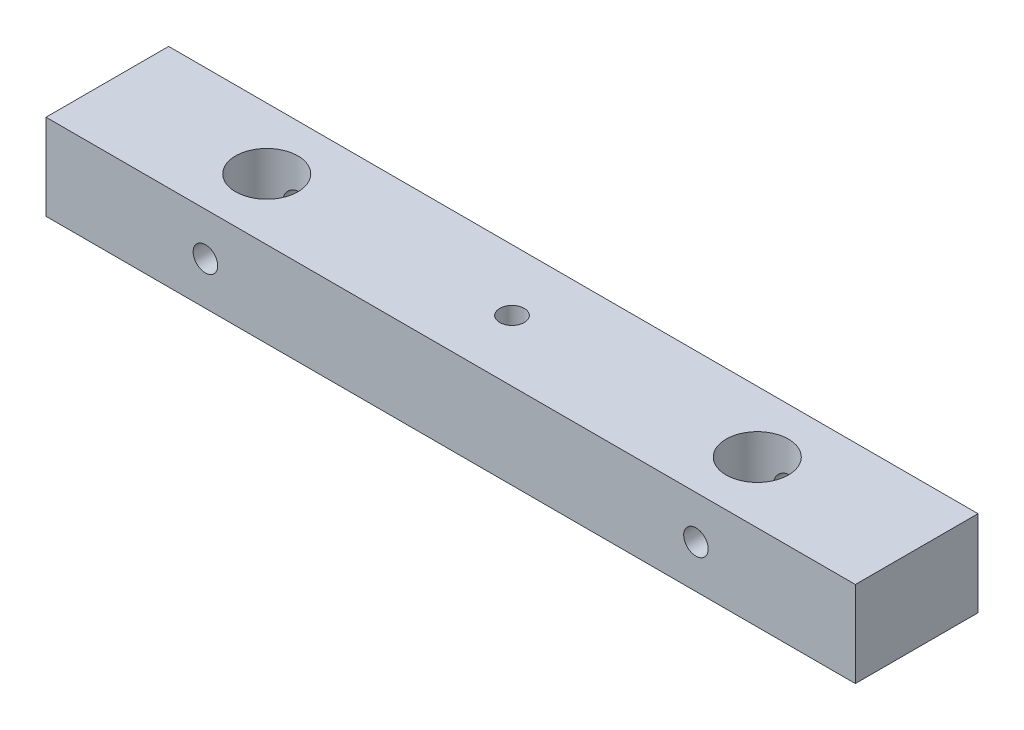
SolidWorks part; units mm, degrees
ref_plane "Front" through (0, 0, 0) normal (0, 0, 1) x (1, 0, 0)
ref_plane "Top" through (0, 0, 0) normal (0, 1, 0) x (1, 0, 0)
ref_plane "Right" through (0, 0, 0) normal (1, 0, 0) x (0, 0, -1)
sketch "Sketch1" plane through (0, 0, 0) normal (0, 1, 0) x (1, 0, 0)
  line L1 (165, 25) -> (-165, 25)
  line L2 (165, 25) -> (165, -25)
  line L3 (165, -25) -> (-165, -25)
  line L4 (-165, 25) -> (-165, -25)
  line L5 (165, 25) -> (-165, -25) construction
  line L6 (165, -25) -> (-165, 25) construction
  point P0 (0, 0)
  dimension "D1" = 330
  dimension "D2" = 50
extrude "Boss-Extrude1" add sketch "Sketch1" along normal blind 35
sketch "Sketch2" plane through (0, 35, 0) normal (0, 1, 0) x (1, 0, 0)
  line L0 (100, 0) -> (-100, 0) construction
  circle A0 centre (-100, 0) radius 12.7
  circle A1 centre (100, 0) radius 12.7
  point P4 (0, 0)
  dimension "D1" = 200
extrude "Cut-Extrude1" cut sketch "Sketch2" against normal blind 70
sketch "Sketch3" plane through (0, 0, 25) normal (0, 0, 1) x (1, 0, 0)
  line L0 (100, 17.5) -> (-100, 17.5) construction
  line L1 (100, 0) -> (100, 35) construction
  line L2 (165, 35) -> (-165, 35) construction
  line L3 (-100, 17.5) -> (-165, 17.5) construction
  line L4 (-165, 0) -> (165, 0) construction
  line L5 (-165, 35) -> (-165, 0) construction
  line L6 (-100, 17.5) -> (-100, 35) construction
  line L7 (-165, 35) -> (165, 35) construction
  circle A0 centre (-100, 17.5) radius 5
  circle A1 centre (100, 17.5) radius 5
  point P4 (0, 17.5)
  point P12 (100, 17.5)
  dimension "D1" = 200
extrude "Cut-Extrude2" cut sketch "Sketch3" against normal blind 70
sketch "Sketch4" plane through (0, 35, 0) normal (0, 1, 0) x (1, 0, 0)
  circle A0 centre (0, 0) radius 5
extrude "Cut-Extrude3" cut sketch "Sketch4" against normal blind 43
